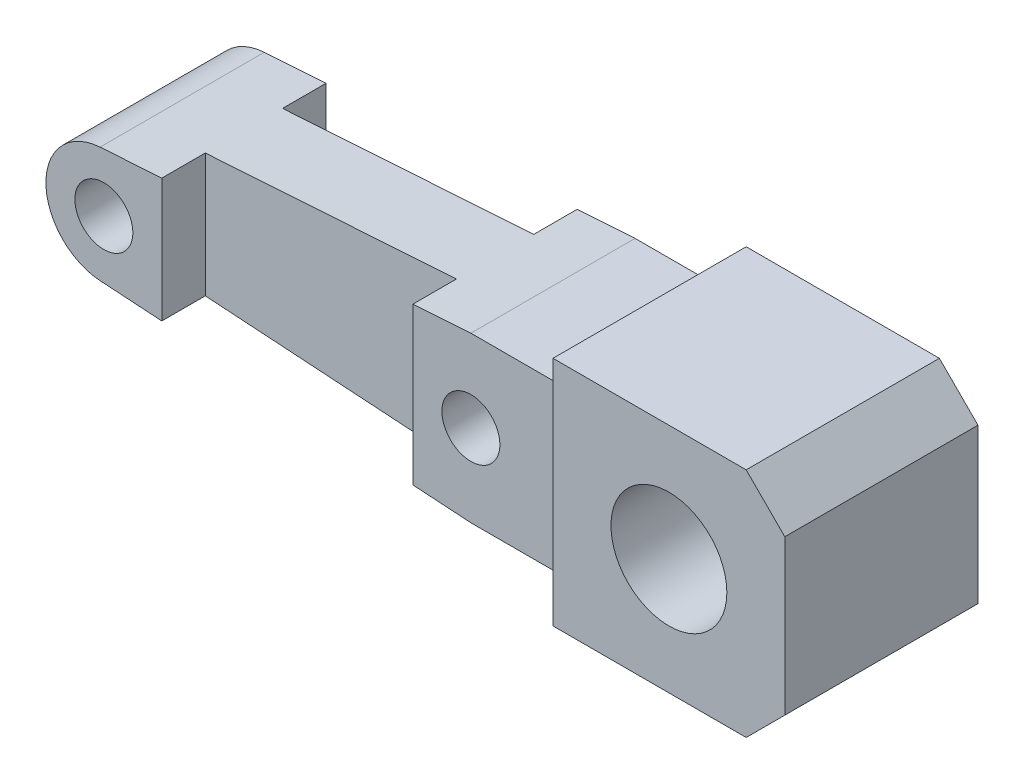
SolidWorks part; units mm, degrees
material "3.0255 (EN-AW 1350A)"
ref_plane "Plan de face" through (0, 0, 0) normal (0, 0, 1) x (1, 0, 0)
ref_plane "Plan de dessus" through (0, 0, 0) normal (0, 1, 0) x (1, 0, 0)
ref_plane "Plan de droite" through (0, 0, 0) normal (1, 0, 0) x (0, 0, -1)
sketch "Esquisse1" plane through (0, 0, 0) normal (0, 0, 1) x (1, 0, 0)
  line L0 (48.5814, 0) -> (-65.7234, 0) construction
  line L1 (8, 12) -> (-12, 12)
  line L2 (12, 8) -> (12, -8)
  line L3 (8, -12) -> (-12, -12)
  line L4 (-12, 12) -> (-12, -12)
  line L5 (12, 12) -> (-12, -12) construction
  line L6 (12, -12) -> (-12, 12) construction
  line L7 (-12, 8.5) -> (-22, 8.5)
  line L8 (-12, 8.5) -> (-12, -8.5)
  line L9 (-12, -8.5) -> (-22, -8.5)
  line L10 (-22, 8.5) -> (-22, 3)
  line L11 (-12, 8.5) -> (-22, -8.5) construction
  line L12 (-12, -8.5) -> (-22, 8.5) construction
  line L13 (0, 37.1212) -> (0, -6.8857) construction
  line L14 (-22, 8.5) -> (-60.3919, 5.9872)
  line L15 (-22, -8.5) -> (-60.3919, -5.9872)
  line L16 (-22, -3) -> (-22, -8.5)
  line L17 (12, 8) -> (8, 12)
  line L18 (12, -8) -> (8, -12)
  circle A0 centre (-22, 0) radius 3
  circle A1 centre (-60, 0) radius 3
  arc A2 (-60.3919, 5.9872) -> (-60.3919, -5.9872) centre (-60, 0) ccw
  circle A3 centre (0, 0) radius 6
  point P0 (0, 0)
  point P6 (-17, 0)
  dimension "D6" = 6
  dimension "D7" = 12
  dimension "D8" = 6
  dimension "D10" = 12
  dimension "D1" = 24
  dimension "D2" = 24
  dimension "D3" = 3.5
  dimension "D4" = 3.5
  dimension "D5" = 10
  dimension "D9" = 38
extrude "Boss.-Extru.1" add sketch "Esquisse1" along normal blind 20 contours L14 A2 L15 L16 A0 L10 A1 | A0 L16 L9 L4 L7 L10 | L18 L2 L17 L1 L4 L3
sketch "Esquisse3" plane through (0, 0, 20) normal (0, 0, 1) x (1, 0, 0)
  line L0 (-12, -8.5) -> (-22, -8.5) construction
  line L1 (-12, 8.5) -> (-28, 8.5)
  line L2 (-12, 8.5) -> (-12, -8.5)
  line L3 (-12, -8.5) -> (-28, -8.5)
  line L4 (-28, 8.5) -> (-28, -8.5)
  line L6 (-78.161, -12.6988) -> (-54, -12.6988)
  line L7 (-78.161, -12.6988) -> (-78.161, 11.2388)
  line L8 (-78.161, 11.2388) -> (-54, 11.2388)
  line L9 (-54, -12.6988) -> (-54, 11.2388)
  dimension "D1" = 16
  dimension "D2" = 26
  dimension "D3" = 23.9376
extrude "Enlèv. mat.-Extru.1" cut sketch "Esquisse3" against normal blind 1.5
sketch "Esquisse4" plane through (0, 0, 20) normal (0, 0, 1) x (1, 0, 0)
  line L1 (-28, 8.1073) -> (-54, 8.1073)
  line L2 (-28, 8.1073) -> (-28, -8.1073)
  line L3 (-28, -8.1073) -> (-54, -8.1073)
  line L4 (-54, 8.1073) -> (-54, -8.1073)
  dimension "D1" = 26
extrude "Enlèv. mat.-Extru.2" cut sketch "Esquisse4" against normal blind 6
ref_plane "Plan1" through (0, 0, 10) normal (0, 0, 1) x (1, 0, 0)
mirror "Symétrie1" about plane through (0, 0, 10) normal (0, 0, 1) of "Enlèv. mat.-Extru.1", "Enlèv. mat.-Extru.2"
ref_plane "Plan2" through (0, 0, 10) normal (0, 0, 1) x (1, 0, 0)
